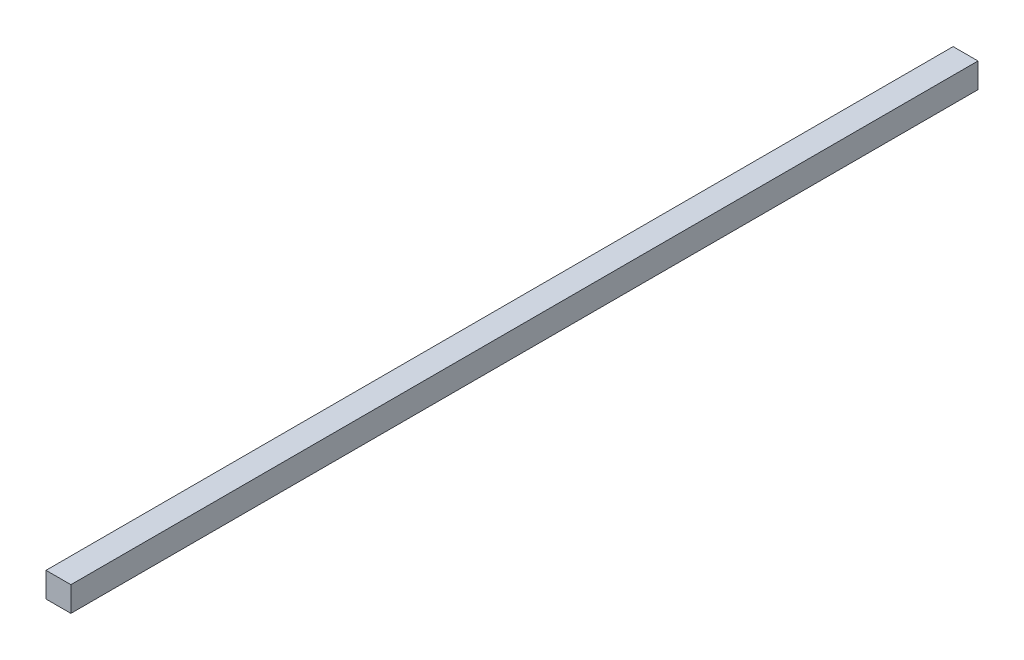
SolidWorks part; units mm, degrees
ref_plane "Front Plane" through (0, 0, 0) normal (0, 0, 1) x (1, 0, 0)
ref_plane "Top Plane" through (0, 0, 0) normal (0, 1, 0) x (1, 0, 0)
ref_plane "Right Plane" through (0, 0, 0) normal (1, 0, 0) x (0, 0, -1)
sketch "Sketch1" plane through (0, 0, 0) normal (0, 0, 1) x (1, 0, 0)
  line L1 (-10, -10) -> (10, -10)
  line L2 (-10, -10) -> (-10, 10)
  line L3 (-10, 10) -> (10, 10)
  line L4 (10, -10) -> (10, 10)
  line L5 (-10, -10) -> (10, 10) construction
  line L6 (-10, 10) -> (10, -10) construction
  point P0 (0, 0)
  dimension "D1" = 20
extrude "Boss-Extrude1" add sketch "Sketch1" along normal mid plane 729
